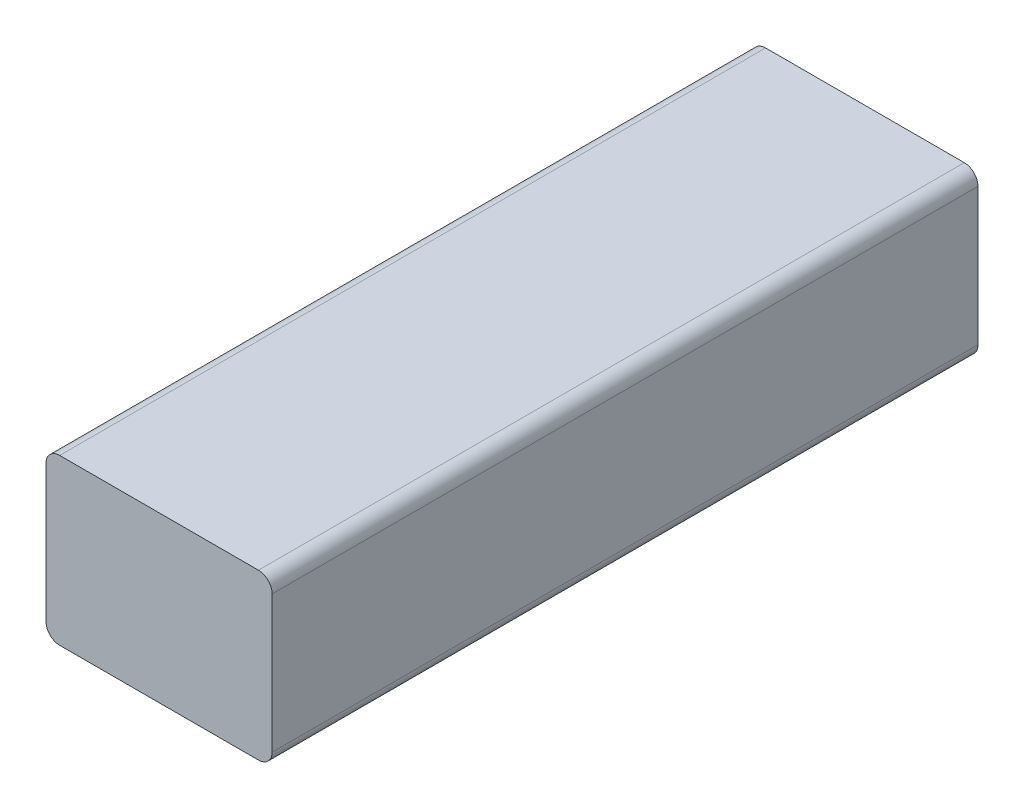
SolidWorks part; units mm, degrees
ref_plane "Front Plane" through (0, 0, 0) normal (0, 0, 1) x (1, 0, 0)
ref_plane "Top Plane" through (0, 0, 0) normal (0, 1, 0) x (1, 0, 0)
ref_plane "Right Plane" through (0, 0, 0) normal (1, 0, 0) x (0, 0, -1)
sketch "Sketch1" plane through (0, 0, 0) normal (0, 1, 0) x (1, 0, 0)
  line L1 (-16.5, -51.5) -> (16.5, -51.5)
  line L2 (-16.5, -51.5) -> (-16.5, 51.5)
  line L3 (-16.5, 51.5) -> (16.5, 51.5)
  line L4 (16.5, -51.5) -> (16.5, 51.5)
  line L5 (-16.5, -51.5) -> (16.5, 51.5) construction
  line L6 (-16.5, 51.5) -> (16.5, -51.5) construction
  point P0 (0, 0)
  dimension "D1" = 103
  dimension "D2" = 33
extrude "Boss-Extrude1" add sketch "Sketch1" along normal blind 24
fillet "Fillet1" radius 2 4 edges at (-16.5, 0, 0) (-16.5, 24, 0) (16.5, 0, 0) (16.5, 24, 0)
